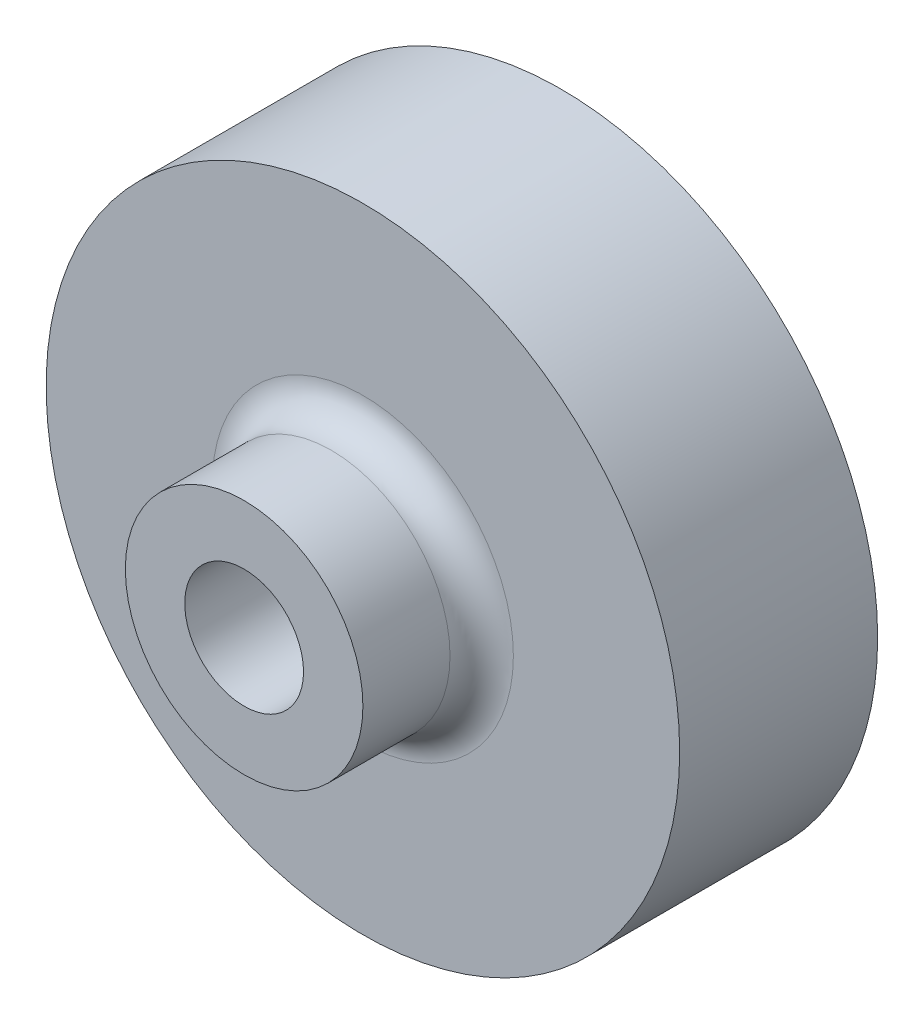
SolidWorks part; units mm, degrees
ref_plane "Front Plane" through (0, 0, 0) normal (0, 0, 1) x (1, 0, 0)
ref_plane "Top Plane" through (0, 0, 0) normal (0, 1, 0) x (1, 0, 0)
ref_plane "Right Plane" through (0, 0, 0) normal (1, 0, 0) x (0, 0, -1)
sketch "Sketch1" plane through (0, 0, 0) normal (0, 0, 1) x (1, 0, 0)
  line L2 (-0.5, 1.8071) -> (-0.5, -1.8071)
  line L4 (0.5, 1.8071) -> (0.5, -1.8071)
  circle A0 centre (0, 0) radius 10
  arc A2 (0.5, -1.8071) -> (0.5, 1.8071) centre (0, 0) ccw
  arc A3 (-0.5, 1.8071) -> (-0.5, -1.8071) centre (0, 0) ccw
  dimension "D1" = 20
  dimension "D2" = 3.75
  dimension "D3" = 1
extrude "Boss-Extrude1" add sketch "Sketch1" along normal blind 1.25 contours L2 A3 | L4 A2 | A0
sketch "Sketch2" plane through (0, 0, 1.25) normal (0, 0, 1) x (1, 0, 0)
  circle A0 centre (0, 0) radius 10
  circle A1 centre (0, 0) radius 1.875
extrude "Boss-Extrude2" add sketch "Sketch2" along normal blind 5
sketch "Sketch3" plane through (0, 0, 6.25) normal (0, 0, 1) x (1, 0, 0)
  circle A0 centre (0, 0) radius 3.75
  circle A1 centre (0, 0) radius 1.875
  dimension "D1" = 7.5
extrude "Boss-Extrude3" add sketch "Sketch3" along normal blind 3.75
fillet "Fillet1" radius 1 1 edges at (3.75, 0, 6.25)
